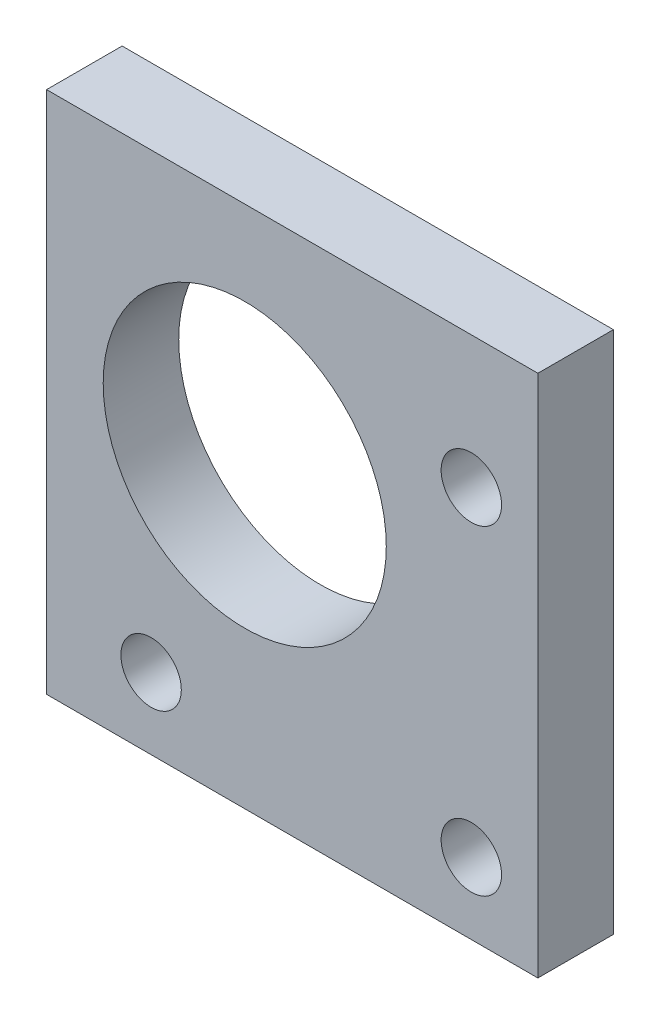
SolidWorks part; units mm, degrees
material "ABS"
ref_plane "Front Plane" through (0, 0, 0) normal (0, 0, 1) x (1, 0, 0)
ref_plane "Top Plane" through (0, 0, 0) normal (0, 1, 0) x (1, 0, 0)
ref_plane "Right Plane" through (0, 0, 0) normal (1, 0, 0) x (0, 0, -1)
sketch "Sketch1" plane through (0, 0, 0) normal (0, 0, 1) x (1, 0, 0)
  line L0 (-14.224, 0) -> (-14.224, -50000) construction
  line L1 (0, 14.224) -> (50000, 14.224) construction
  line L2 (-7.874, -19.05) -> (-14.224, -19.05) construction
  line L3 (19.05, 7.874) -> (19.05, 14.224) construction
  line L4 (-7.874, -19.05) -> (19.05, -19.05) construction
  line L5 (19.05, -19.05) -> (19.05, 7.874) construction
  line L7 (24.6442, -25.0416) -> (-16.6592, -25.0416)
  line L8 (24.6442, -25.0416) -> (24.6442, 18.9902)
  line L9 (24.6442, 18.9902) -> (-16.6592, 18.9902)
  line L10 (-16.6592, -25.0416) -> (-16.6592, 18.9902)
  circle A0 centre (0, 0) radius 11.8999
  circle A1 centre (0, 0) radius 14.224 construction
  circle A2 centre (19.05, 7.874) radius 2.54
  circle A3 centre (19.05, -19.05) radius 2.54
  circle A4 centre (-7.874, -19.05) radius 2.54
  dimension "D1" = 23.7998
  dimension "D3" = 5.08
  dimension "D6" = 19.05
  dimension "D2" = 28.448
  dimension "D4" = 6.35
  dimension "D5" = 19.05
extrude "Boss-Extrude1" add sketch "Sketch1" along normal blind 6.35
